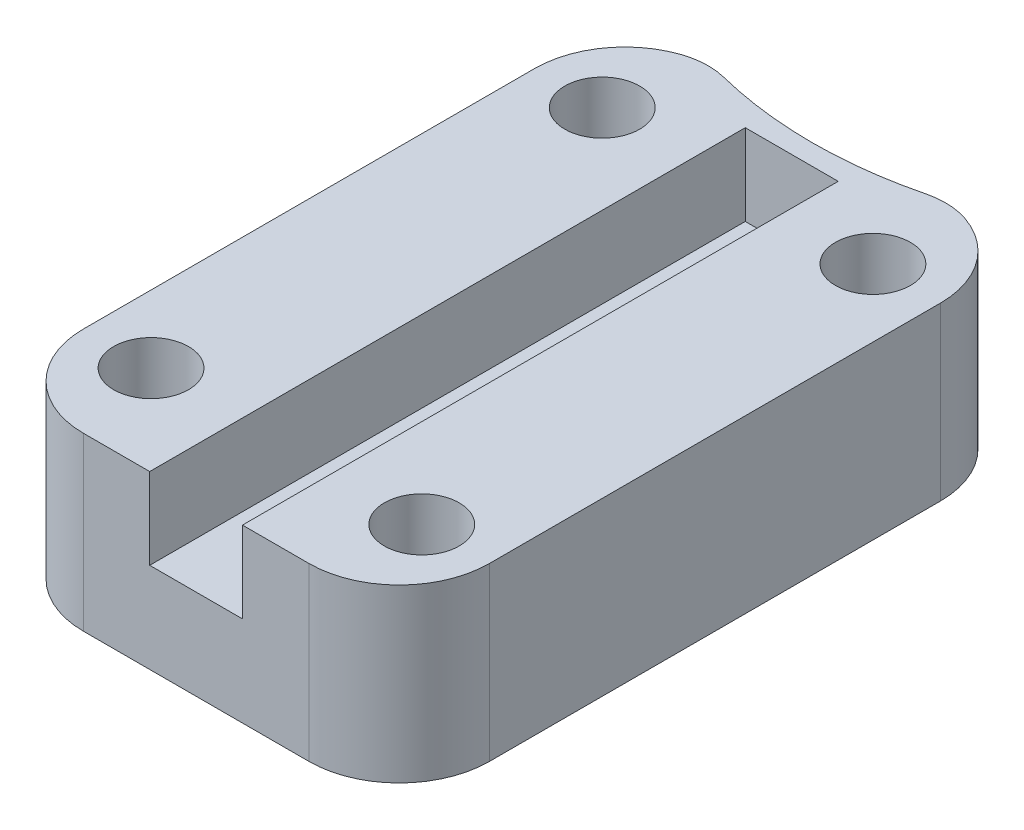
SolidWorks part; units mm, degrees
ref_plane "Спереди" through (0, 0, 0) normal (0, 0, 1) x (1, 0, 0)
ref_plane "Сверху" through (0, 0, 0) normal (0, 1, 0) x (1, 0, 0)
ref_plane "Справа" through (0, 0, 0) normal (1, 0, 0) x (0, 0, -1)
sketch "Sketch1" plane through (0, 0, 0) normal (0, 1, 0) x (1, 0, 0)
  line L1 (22.5, -35) -> (-22.5, -35)
  line L2 (22.5, -35) -> (22.5, 35)
  line L3 (22.5, 35) -> (-22.5, 35)
  line L4 (-22.5, -35) -> (-22.5, 35)
  line L5 (22.5, -35) -> (-22.5, 35) construction
  line L6 (22.5, 35) -> (-22.5, -35) construction
  point P0 (0, 0)
  dimension "D1" = 45
  dimension "D2" = 70
extrude "Boss-Extrude1" add sketch "Sketch1" along normal blind 10
sketch "Sketch3" plane through (0, 0, 0) normal (0, -1, 0) x (1, 0, 0)
  line L0 (15, -25) -> (15, 25) construction
  line L1 (-15, 25) -> (-15, -25) construction
  line L2 (-15, -25) -> (15, 25) construction
  line L3 (-22.5, -25) -> (22.5, -25) construction
  line L4 (-22.5, -35) -> (-22.5, 35) construction
  line L5 (22.5, 35) -> (22.5, -35) construction
  line L6 (-22.5, 25) -> (22.5, 25) construction
  line L7 (-22.5, -35) -> (-22.5, 35) construction
  line L8 (22.5, 35) -> (22.5, -35) construction
  line L9 (-15, 25) -> (15, -25) construction
  circle A0 centre (15, 25) radius 4.15
  circle A1 centre (15, -25) radius 4.15
  circle A2 centre (-15, -25) radius 4.15
  circle A3 centre (-15, 25) radius 4.15
  point P4 (0, 0)
  dimension "D1" = 8.3
  dimension "D2" = 30
  dimension "D3" = 50
extrude "Cut-Extrude2" cut sketch "Sketch3" against normal through all
sketch "Sketch5" plane through (0, 10, 0) normal (0, 1, 0) x (1, 0, 0)
  line L0 (5.15, 35) -> (-5.15, -35) construction
  line L1 (-5.15, -35) -> (-22.5, -35)
  line L2 (-5.15, -35) -> (-5.15, 35) construction
  line L3 (-5.15, 35) -> (-22.5, 35) construction
  line L4 (-22.5, -35) -> (-22.5, 35)
  line L5 (-5.15, -35) -> (-22.5, 35) construction
  line L6 (-5.15, 35) -> (-22.5, -35) construction
  line L7 (5.15, -35) -> (22.5, -35)
  line L8 (5.15, -35) -> (5.15, 35) construction
  line L9 (5.15, 35) -> (22.5, 35) construction
  line L10 (22.5, -35) -> (22.5, 35)
  line L11 (5.15, -35) -> (22.5, 35) construction
  line L12 (5.15, 35) -> (22.5, -35) construction
  line L13 (5.15, -35) -> (-5.15, 35) construction
  line L14 (-5.15, -35) -> (-5.15, 31)
  line L15 (-5.15, 31) -> (5.15, 31)
  line L16 (5.15, 31) -> (5.1302, -34.9493)
  line L17 (5.15, -35) -> (5.1302, -34.9493)
  line L18 (-22.5, 35) -> (22.5, 35)
  circle A0 centre (-15, 25) radius 4.15
  circle A1 centre (15, 25) radius 4.15
  circle A2 centre (15, -25) radius 4.15
  circle A3 centre (-15, -25) radius 4.15
  point P0 (-13.825, 0)
  point P6 (13.825, 0)
  point P12 (0, 0)
  dimension "D1" = 10.3
  dimension "D2" = 4
extrude "Boss-Extrude2" add sketch "Sketch5" along normal blind 9
chamfer "Chamfer1" distance 1 angle 50 4 edges at (15, 0, 20.85) (-15, 0, 20.85) (-15, 0, -29.15) (15, 0, -29.15)
fillet "Fillet1" radius 10 4 edges at (22.5, 9.5, 35) (-22.5, 9.5, 35) (-22.5, 9.5, -35) (22.5, 9.5, -35)
sketch "Sketch6" plane through (0, 19, 0) normal (0, 1, 0) x (1, 0, 0)
  line L0 (-12.5, 35) -> (12.5, 35)
  arc A0 (-12.5, 35) -> (12.5, 35) centre (0, 79.2691) ccw
  dimension "D1" = 46
extrude "Cut-Extrude3" cut sketch "Sketch6" against normal through all
fillet "Fillet2" radius 8 2 edges at (-12.5, 9.5, -35) (12.5, 9.5, -35)
